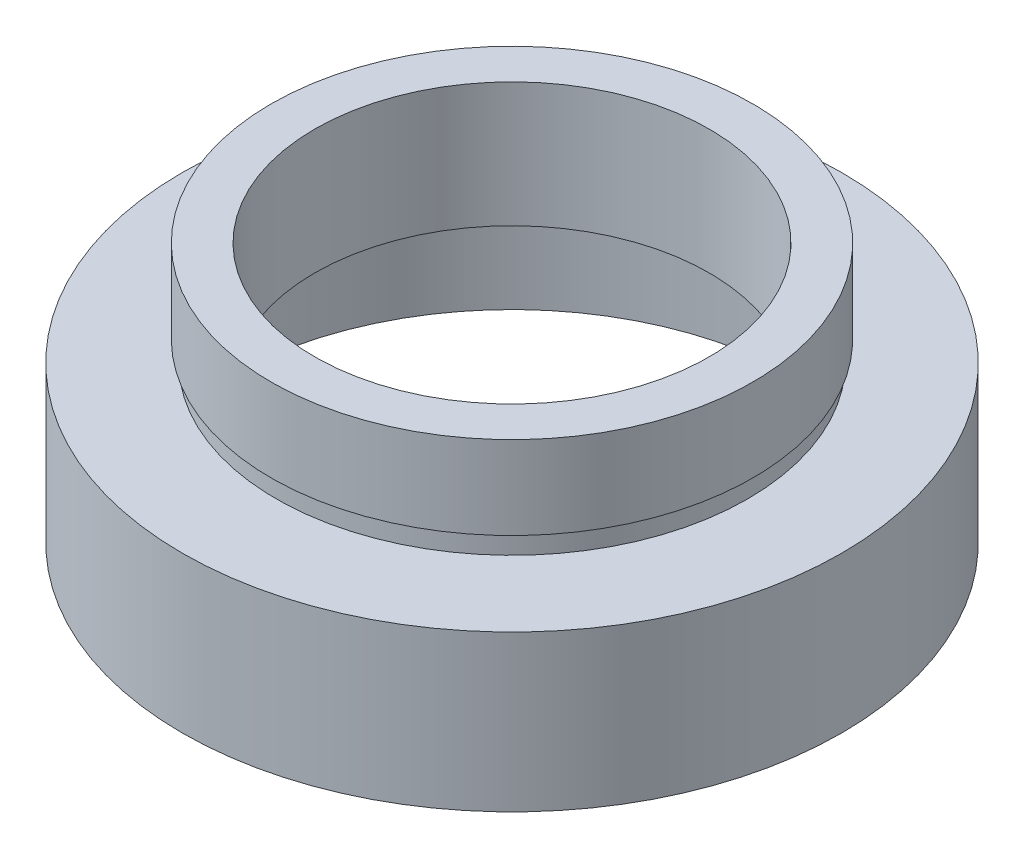
SolidWorks part; units mm, degrees
ref_plane "前视基准面" through (0, 0, 0) normal (0, 0, 1) x (1, 0, 0)
ref_plane "上视基准面" through (0, 0, 0) normal (0, 1, 0) x (1, 0, 0)
ref_plane "右视基准面" through (0, 0, 0) normal (1, 0, 0) x (0, 0, -1)
sketch "草图1" plane through (0, 0, 0) normal (0, 0, 1) x (1, 0, 0)
  line L0 (0, 16.886) -> (0, -24.4878) construction
  line L1 (13.75, 0) -> (13.75, 5.5)
  line L2 (9.5, 6.5) -> (14.35, 6.5)
  line L3 (9.5, 6.5) -> (9.5, 12.5)
  line L4 (9.5, 12.5) -> (11.6, 12.5)
  line L5 (11.6, 12.5) -> (11.6, 8.5)
  line L6 (11.6, 8.5) -> (11.35, 8.5)
  line L7 (11.35, 8.5) -> (11.35, 7.5)
  line L8 (11.35, 7.5) -> (15.875, 7.5)
  line L9 (15.875, 7.5) -> (15.875, 0)
  line L10 (15.875, 0) -> (13.75, 0)
  line L11 (13.75, 5.5) -> (14.35, 5.5)
  line L12 (14.35, 5.5) -> (14.35, 6.5)
  line L13 (0, 0) -> (3.4668, 0) construction
  point P4 (14.8125, 0)
  dimension "D1" = 9.5
  dimension "D2" = 11.6
  dimension "D3" = 11.35
  dimension "D4" = 13.75
  dimension "D5" = 14.35
  dimension "D6" = 15.875
  dimension "D7" = 12.5
  dimension "D8" = 7.5
  dimension "D9" = 1
  dimension "D10" = 5.5
  dimension "D11" = 1
revolve "旋转1" add sketch "草图1" angle 360 about L0
cosmetic thread "装饰螺纹线1" parameters "D2"=22.2
cosmetic thread "装饰螺纹线2" parameters "D2"=20
cosmetic thread "装饰螺纹线3" parameters "D2"=28.5
